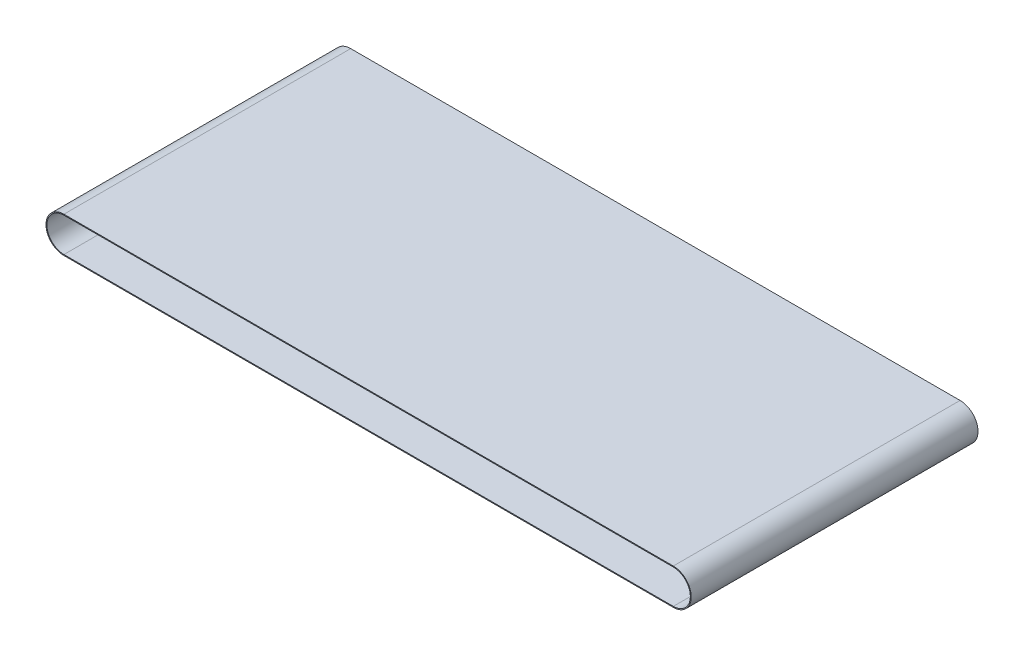
SolidWorks part; units mm, degrees
ref_plane "Alzado" through (0, 0, 0) normal (0, 0, 1) x (1, 0, 0)
ref_plane "Planta" through (0, 0, 0) normal (0, 1, 0) x (1, 0, 0)
ref_plane "Vista lateral" through (0, 0, 0) normal (1, 0, 0) x (0, 0, -1)
sketch "Croquis1" plane through (0, 0, 0) normal (0, 0, 1) x (1, 0, 0)
  line L0 (-425, 0) -> (425, 0) construction
  line L1 (-425, 23.75) -> (425, 23.75)
  line L2 (-425, -23.75) -> (425, -23.75)
  line L3 (-425, 25) -> (425, 25)
  line L4 (-425, -25) -> (425, -25)
  arc A0 (-425, 23.75) -> (-425, -23.75) centre (-425, 0) ccw
  arc A1 (425, -23.75) -> (425, 23.75) centre (425, 0) ccw
  arc A2 (-425, 25) -> (-425, -25) centre (-425, 0) ccw
  arc A3 (425, -25) -> (425, 25) centre (425, 0) ccw
  point P4 (0, 0)
  dimension "D2" = 47.5
  dimension "D3" = 47.5
  dimension "D4" = 50
  dimension "D5" = 50
  dimension "D1" = 850
extrude "Saliente-Extruir1" add sketch "Croquis1" along normal blind 400
